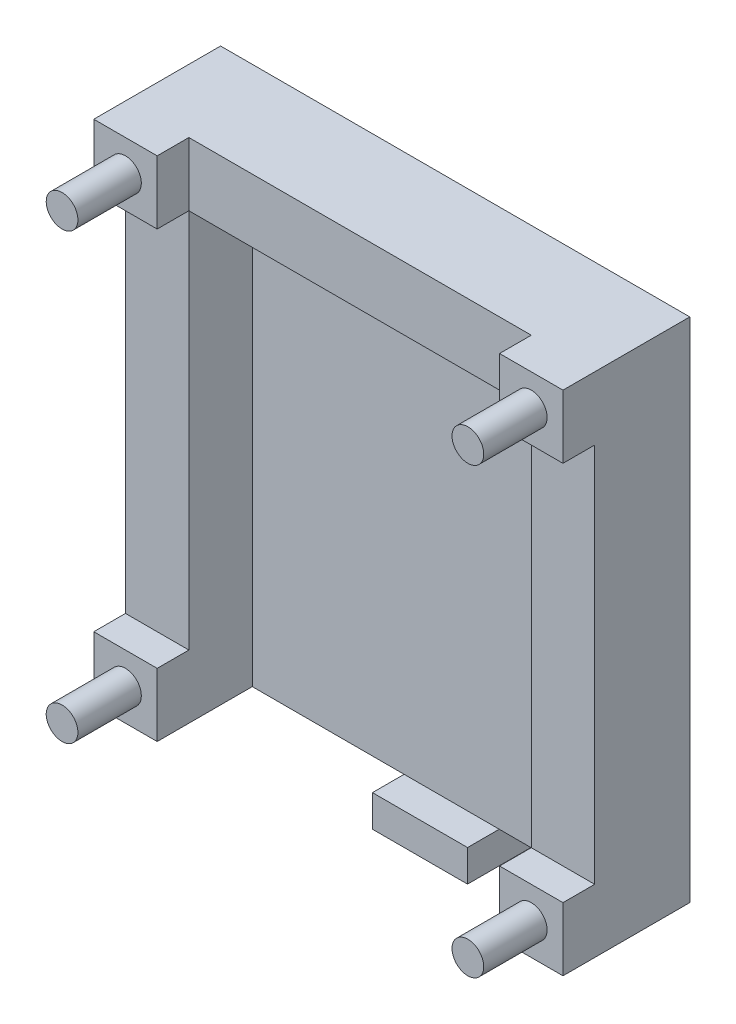
SolidWorks part; units mm, degrees
ref_plane "Alzado" through (0, 0, 0) normal (0, 0, 1) x (1, 0, 0)
ref_plane "Planta" through (0, 0, 0) normal (0, 1, 0) x (1, 0, 0)
ref_plane "Vista lateral" through (0, 0, 0) normal (1, 0, 0) x (0, 0, -1)
sketch "Croquis1" plane through (0, 0, 0) normal (0, 0, 1) x (1, 0, 0)
  line L0 (1.4005, 36.5086) -> (55.4005, 36.5086)
  line L1 (55.4005, 36.5086) -> (55.4005, -33.4914)
  line L2 (55.4005, -33.4914) -> (1.4005, -33.4914)
  line L3 (1.4005, -33.4914) -> (1.4005, 36.5086)
  dimension "D1" = 54
  dimension "D2" = 70
extrude "Saliente-Extruir1" add sketch "Croquis1" along normal blind 5
sketch "Croquis2" plane through (0, 0, 5) normal (0, 0, 1) x (1, 0, 0)
  line L0 (1.4005, 36.5086) -> (-8.0995, 36.5086)
  line L1 (55.4005, 36.5086) -> (1.4005, 36.5086) construction
  line L2 (55.4005, 36.5086) -> (1.4005, 36.5086)
  line L3 (1.4005, 36.5086) -> (1.4005, -33.4914)
  line L4 (1.4005, -33.4914) -> (55.4005, -33.4914) construction
  line L5 (1.4005, -33.4914) -> (-8.0995, -33.4914)
  line L6 (-8.0995, -33.4914) -> (-8.0995, 36.5086)
  line L7 (1.4005, 36.5086) -> (-8.0995, 36.5086)
sketch "Croquis4" plane through (0, 0, 0) normal (0, 0, -1) x (-1, 0, 0)
  line L0 (-55.4005, 36.5086) -> (-55.4005, 46.5086)
  line L1 (-55.4005, 46.5086) -> (-1.4005, 46.5086)
  line L2 (-1.4005, 46.5086) -> (-1.4005, 36.5086)
  line L3 (-1.4005, 36.5086) -> (-55.4005, 36.5086)
  dimension "D1" = 10
extrude "Saliente-Extruir5" add sketch "Croquis4" against normal blind 15
sketch "Croquis5" plane through (0, 0, 0) normal (0, 0, -1) x (-1, 0, 0)
  line L0 (-55.4005, 46.5086) -> (-65.4005, 46.5086)
  line L1 (-65.4005, 46.5086) -> (-65.4005, 36.5086)
  line L2 (-65.4005, 36.5086) -> (-55.4005, 36.5086)
  line L3 (-55.4005, 36.5086) -> (-55.4005, 46.5086)
  line L4 (-55.4005, 46.5086) -> (-28.4005, 46.5086)
  line L5 (-1.4005, 46.5086) -> (-55.4005, 46.5086) construction
  line L6 (-28.4005, 46.5086) -> (-28.4005, 24.5969)
  line L7 (-55.4005, -33.4914) -> (-65.4005, -33.4914)
  line L8 (-65.4005, -33.4914) -> (-65.4005, -23.4914)
  line L9 (-65.4005, -23.4914) -> (-55.4005, -23.4914)
  line L10 (-55.4005, -33.4914) -> (-55.4005, 46.5086) construction
  line L11 (-55.4005, -23.4914) -> (-55.4005, -33.4914)
  line L12 (-55.4005, -33.4914) -> (-55.597, -33.6261)
  line L13 (-1.4005, -23.4914) -> (-1.4005, -33.4914)
  line L14 (8.5995, -23.4914) -> (-1.4005, -23.4914)
  line L15 (8.5995, -33.4914) -> (8.5995, -23.4914)
  line L16 (-1.4005, -33.4914) -> (8.5995, -33.4914)
  line L17 (-1.4005, 36.5086) -> (-1.4005, 46.5086)
  line L18 (8.5995, 36.5086) -> (-1.4005, 36.5086)
  line L19 (8.5995, 46.5086) -> (8.5995, 36.5086)
  line L20 (-1.4005, 46.5086) -> (8.5995, 46.5086)
  line L21 (-1.4005, -33.4914) -> (-1.2041, -33.6261)
  line M1 (-1.4005, -33.4914) -> (-1.4005, 46.5086)
  line M3 (-55.4005, 46.5086) -> (-55.4005, -33.4914)
extrude "Saliente-Extruir6" add sketch "Croquis5" against normal blind 20 contours L1 L2 L0 M3 | L9 L8 L7 M3 | L16 L15 L14 M1 | L20 L18 L19 M1
sketch "Croquis6" plane through (0, 0, 0) normal (0, 0, -1) x (-1, 0, 0)
  line L1 (8.5995, -33.4914) -> (-65.4005, -33.4914) construction
  line L3 (-40.349, -38.4914) -> (-40.349, -33.4914)
  line L4 (-40.349, -33.4914) -> (-25.349, -33.4914)
  line L5 (-25.349, -33.4914) -> (-25.349, -38.4914)
  line L6 (-25.349, -38.4914) -> (-40.349, -38.4914)
  dimension "D1" = 5
  dimension "D4" = 15
extrude "Saliente-Extruir7" add sketch "Croquis6" against normal blind 10 separate body
sketch "Croquis8" plane through (0, 0, 0) normal (0, 0, -1) x (-1, 0, 0)
  line L0 (-65.4005, 36.5086) -> (-65.4005, -23.4914)
  line L1 (-65.4005, -23.4914) -> (-55.4005, -23.4914)
  line L2 (-55.4005, -23.4914) -> (-55.4005, 36.5086)
  line L3 (-55.4005, 36.5086) -> (-65.4005, 36.5086)
  line L4 (-28.4005, 46.5086) -> (-28.4005, 34.2655)
  line L5 (8.5995, 46.5086) -> (-65.4005, 46.5086) construction
  line L6 (-1.4005, 36.5086) -> (8.5995, 36.5086)
  line L7 (-1.4005, -23.4914) -> (-1.4005, 36.5086)
  line L8 (8.5995, -23.4914) -> (-1.4005, -23.4914)
  line L9 (8.5995, 36.5086) -> (8.5995, -23.4914)
  line M1 (-1.4005, -23.4914) -> (-1.4005, 36.5086)
  line M2 (-1.4005, 36.5086) -> (8.5995, 36.5086)
  line M6 (-65.4005, 36.5086) -> (-55.4005, 36.5086)
  line M7 (-55.4005, 36.5086) -> (-55.4005, -23.4914)
  line M8 (-55.4005, -23.4914) -> (-65.4005, -23.4914)
  line M12 (8.5995, -23.4914) -> (-1.4005, -23.4914)
extrude "Saliente-Extruir9" add sketch "Croquis8" against normal blind 15 contours L0 M6 M8 M7 | L9 M2 M1 M12
sketch "Croquis9" plane through (0, 0, 20) normal (0, 0, 1) x (1, 0, 0)
  line L0 (-8.5995, 46.5086) -> (-8.5995, 36.5086)
  line L1 (-8.5995, 46.5086) -> (-8.5995, 36.5086) construction
  line L2 (-8.5995, 41.5086) -> (1.4005, 41.5086)
  line L3 (1.4005, 36.5086) -> (1.4005, 46.5086) construction
  line L4 (-8.5995, 46.5086) -> (-8.5995, 6.5086)
  line L5 (-8.5995, 36.5086) -> (-8.5995, -23.4914) construction
  line L6 (-8.5995, 6.5086) -> (65.4005, 6.5086)
  line L7 (65.4005, 36.5086) -> (65.4005, -23.4914) construction
  line L8 (65.4005, 6.5086) -> (28.4005, 6.5086)
  line L9 (28.4005, 6.5086) -> (28.4005, 19.0549)
  circle A0 centre (-3.5995, 41.5086) radius 2.5
  circle A1 centre (60.4005, 41.5086) radius 2.5
  circle A2 centre (60.4005, -28.4914) radius 2.5
  circle A3 centre (-3.5995, -28.4914) radius 2.5
  dimension "D1" = 5
extrude "Saliente-Extruir10" add sketch "Croquis9" along normal blind 10 contours L2 A0 | L2 A0 | A1 | A2 | A3
sketch "Croquis11" plane through (0, 0, 0) normal (0, 0, -1) x (-1, 0, 0)
  line L0 (-65.4005, 46.5086) -> (-65.4005, 36.5086)
  line L1 (-65.4005, 36.5086) -> (-65.4005, 41.5086)
  line L2 (-65.4005, 41.5086) -> (-60.4005, 41.5086)
  line L3 (-60.4005, 41.5086) -> (8.5995, 41.5086)
  line L4 (8.5995, -33.4914) -> (8.5995, 46.5086) construction
  line L5 (8.5995, 41.5086) -> (-25.9005, 41.5086)
  line L6 (-65.4005, 46.5086) -> (-65.4005, 6.5086)
  line L7 (-65.4005, 46.5086) -> (-65.4005, -33.4914) construction
  line L8 (-65.4005, 6.5086) -> (-25.349, 6.5086)
  line L9 (-25.349, 6.5086) -> (8.5995, 6.5086)
  line L10 (-65.4005, -33.4914) -> (-28.4005, -33.4914)
  line L12 (8.5995, -33.4914) -> (-65.4005, -33.4914) construction
  line L13 (-28.4005, -33.4914) -> (-28.4005, 6.5086)
  circle A0 centre (-60.4005, 41.5086) radius 2.55
  circle A1 centre (-60.4005, -28.4914) radius 2.55
  circle A2 centre (3.5995, -28.4914) radius 2.55
  circle A3 centre (3.5995, 41.5086) radius 2.55
  dimension "D1" = 40.0516
  dimension "D2" = 5.1
extrude "Cortar-Extruir1" cut sketch "Croquis11" against normal blind 10 contours L3 A0 L2 | L2 A0 L3 | A3 L5 | A3 L5 | A2 | A1
